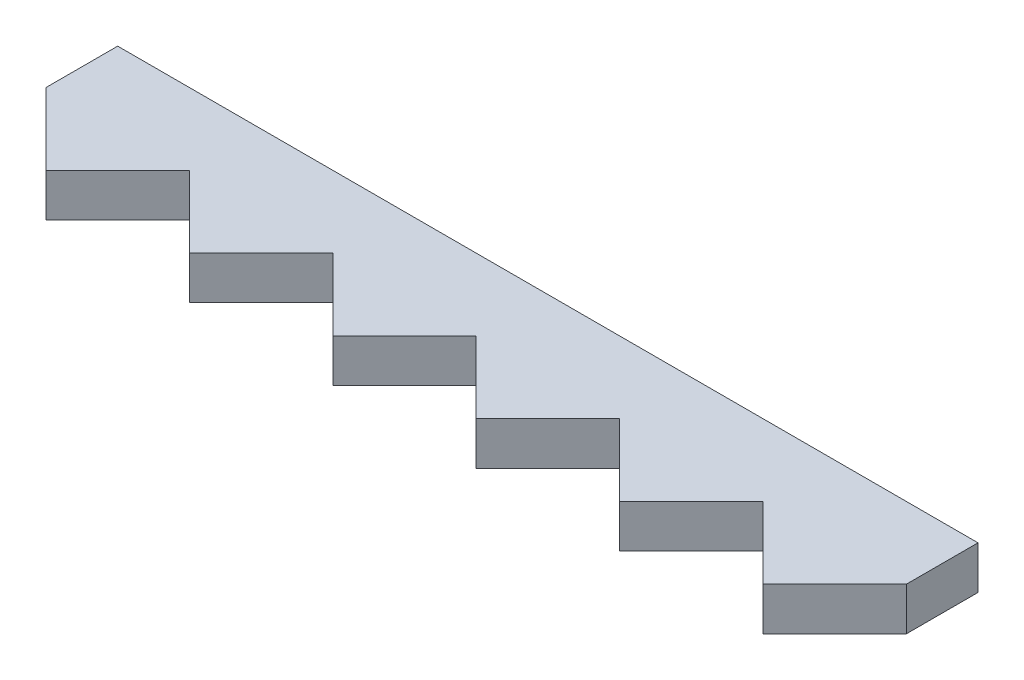
SolidWorks part; units mm, degrees
material "Custom Plastic"
ref_plane "Front Plane" through (0, 0, 0) normal (0, 0, 1) x (1, 0, 0)
ref_plane "Top Plane" through (0, 0, 0) normal (0, 1, 0) x (1, 0, 0)
ref_plane "Right Plane" through (0, 0, 0) normal (1, 0, 0) x (0, 0, -1)
sketch "Sketch1" plane through (0, 3, 0) normal (0, 1, 0) x (1, 0, 0)
  line L0 (0, 71.6064) -> (0, 66.6064)
  line L1 (50, 66.6064) -> (55, 61.6064)
  line L2 (0, 66.6064) -> (5, 61.6064)
  line L3 (5, 61.6064) -> (10, 66.6064)
  line L4 (55, 61.6064) -> (60, 66.6064)
  line L5 (60, 66.6064) -> (60, 71.6064)
  line L7 (10, 66.6064) -> (15, 61.6064)
  line L8 (15, 61.6064) -> (20, 66.6064)
  line L9 (20, 66.6064) -> (25, 61.6064)
  line L10 (25, 61.6064) -> (30, 66.6064)
  line L11 (30, 66.6064) -> (35, 61.6064)
  line L12 (35, 61.6064) -> (40, 66.6064)
  line L13 (40, 66.6064) -> (45, 61.6064)
  line L14 (45, 61.6064) -> (50, 66.6064)
  line L19 (0, 71.6064) -> (60, 71.6064)
  point P8 (59.1088, 71.6064)
  dimension "D1" = 5
  dimension "D2" = 5
  dimension "D3" = 10
  dimension "D4" = 6
extrude "Boss-Extrude1" add sketch "Sketch1" along normal blind 3
